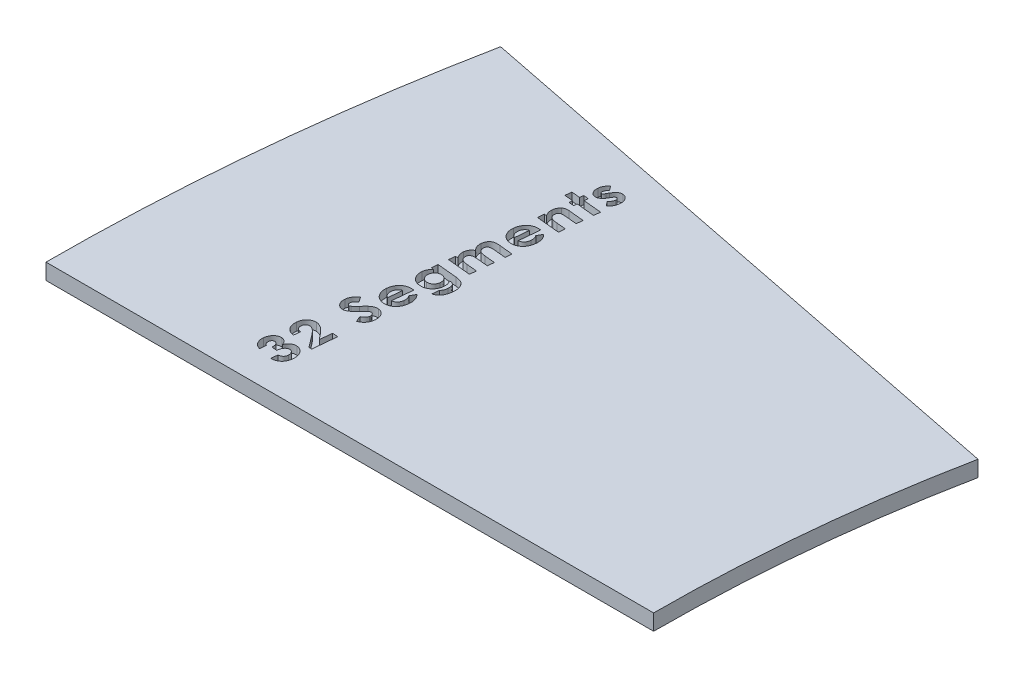
SolidWorks part; units mm, degrees
ref_plane "Front Plane" through (0, 0, 0) normal (0, 0, 1) x (1, 0, 0)
ref_plane "Top Plane" through (0, 0, 0) normal (0, 1, 0) x (1, 0, 0)
ref_plane "Right Plane" through (0, 0, 0) normal (1, 0, 0) x (0, 0, -1)
sketch "Sketch1" plane through (0, 0, 0) normal (0, 1, 0) x (1, 0, 0)
  line L0 (0, 0) -> (121.1983, 0)
  line L1 (127, 58.9054) -> (8.1305, 82.55)
  arc A0 (0, 0) -> (8.1305, 82.55) centre (423.1373, 0) cw
  arc A1 (121.1983, 0) -> (127, 58.9054) centre (423.1373, 0) cw
  dimension "D1" = 11.25
  dimension "D2" = 82.55
  dimension "D3" = 127
extrude "Boss-Extrude1" add sketch "Sketch1" along normal blind 3.175
sketch "Sketch2" plane through (0, 3.175, 0) normal (0, 1, 0) x (1, 0, 0)
  line L0 (40.386, 0) -> (47.7405, 74.6711) construction
  line L1 (0, 0) -> (121.1983, 0) construction
  line L2 (127, 58.9054) -> (8.1305, 82.55) construction
  text T0 "<b>32 Segments</b>" font "Century Gothic" height in points 24
  dimension "D1" = 40.386
  dimension "D2" = 40.386
extrude "Cut-Extrude1" cut sketch "Sketch2" against normal blind 1.5875
